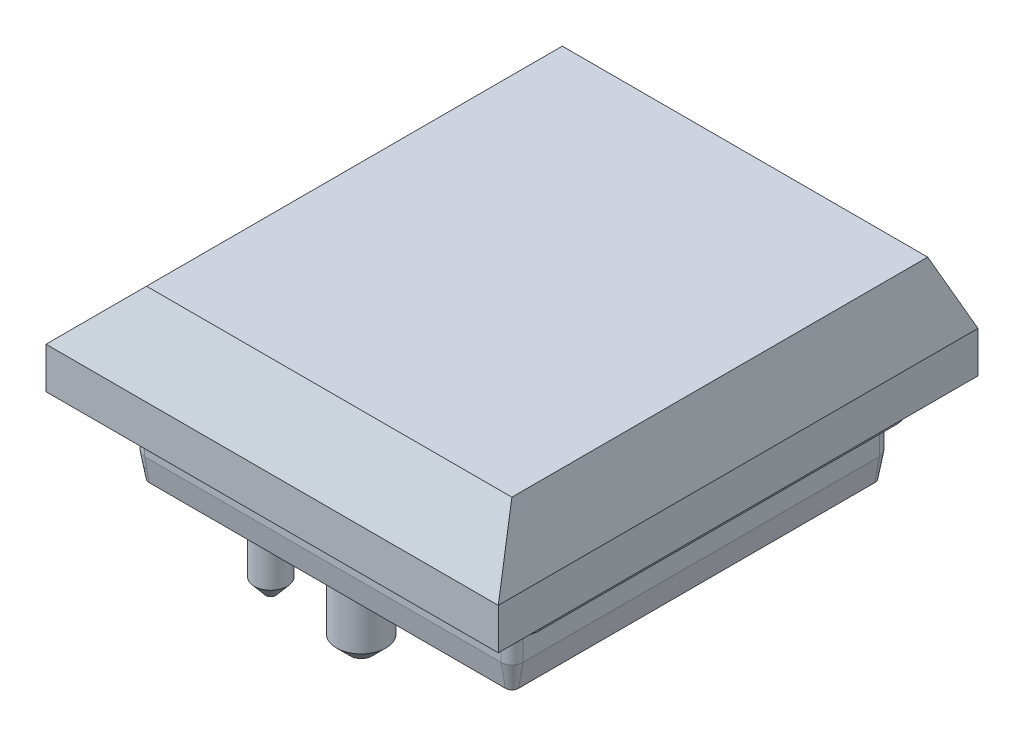
SolidWorks part; units mm, degrees
ref_plane "Front plane" through (0, 0, 0) normal (0, 0, 1) x (1, 0, 0)
ref_plane "Top plane" through (0, 0, 0) normal (0, 1, 0) x (1, 0, 0)
ref_plane "Right plane" through (0, 0, 0) normal (1, 0, 0) x (0, 0, -1)
sketch "Sketch1" plane through (0, 0, 0) normal (0, 1, 0) x (1, 0, 0)
  line L1 (-6.5, -7.5) -> (6.5, -7.5)
  line L2 (-7.5, -6.5) -> (-7.5, 6.5)
  line L3 (-6.5, 7.5) -> (6.5, 7.5)
  line L4 (7.5, -6.5) -> (7.5, 6.5)
  line L5 (-7.5, -7.5) -> (7.5, 7.5) construction
  line L6 (-7.5, 7.5) -> (7.5, -7.5) construction
  arc A0 (-7.5, 6.5) -> (-6.5, 7.5) centre (-6.5, 6.5) cw
  arc A1 (6.5, 7.5) -> (7.5, 6.5) centre (6.5, 6.5) cw
  arc A2 (6.5, -7.5) -> (7.5, -6.5) centre (6.5, -6.5) ccw
  arc A3 (-6.5, -7.5) -> (-7.5, -6.5) centre (-6.5, -6.5) cw
  point P0 (0, 0)
  dimension "D2" = 1
  dimension "D1" = 15
extrude "Boss-Extrude1" add sketch "Sketch1" along normal blind 0.8 contours L1 A2 L4 A1 L3 A0 L2 A3
sketch "Sketch2" plane through (0, 0, 0) normal (0, -1, 0) x (1, 0, 0)
  line L8 (-6.9, 6.5) -> (-6.9, -6.5)
  line L9 (-6.5, -6.9) -> (6.5, -6.9)
  line L10 (6.9, -6.5) -> (6.9, 6.5)
  line L11 (6.5, 6.9) -> (-6.5, 6.9)
  line L12 (-6.9, 6.5) -> (-6.9, -6.5)
  line L13 (-6.5, -6.9) -> (6.5, -6.9)
  line L14 (6.9, -6.5) -> (6.9, 6.5)
  line L15 (6.5, 6.9) -> (-6.5, 6.9)
  arc A8 (-6.5, 6.9) -> (-6.9, 6.5) centre (-6.5, 6.5) ccw
  arc A9 (-6.9, -6.5) -> (-6.5, -6.9) centre (-6.5, -6.5) ccw
  arc A10 (6.5, -6.9) -> (6.9, -6.5) centre (6.5, -6.5) ccw
  arc A11 (6.9, 6.5) -> (6.5, 6.9) centre (6.5, 6.5) ccw
  arc A12 (-6.5, 6.9) -> (-6.9, 6.5) centre (-6.5, 6.5) ccw
  arc A13 (-6.9, -6.5) -> (-6.5, -6.9) centre (-6.5, -6.5) ccw
  arc A14 (6.5, -6.9) -> (6.9, -6.5) centre (6.5, -6.5) ccw
  arc A15 (6.9, 6.5) -> (6.5, 6.9) centre (6.5, 6.5) ccw
  dimension "D1" = 0.6
extrude "Boss-Extrude2" add sketch "Sketch2" along normal blind 1.3
sketch "Sketch3" plane through (0, -1.3, 0) normal (0, -1, 0) x (1, 0, 0)
  line L4 (-6.9, 6.5) -> (-6.9, -6.5)
  line L5 (-6.5, -6.9) -> (6.5, -6.9)
  line L6 (6.9, -6.5) -> (6.9, 6.5)
  line L7 (6.5, 6.9) -> (-6.5, 6.9)
  line L8 (-6.9, 6.5) -> (-6.9, -6.5)
  line L9 (-6.5, -6.9) -> (6.5, -6.9)
  line L10 (6.9, -6.5) -> (6.9, 6.5)
  line L11 (6.5, 6.9) -> (-6.5, 6.9)
  arc A4 (-6.5, 6.9) -> (-6.9, 6.5) centre (-6.5, 6.5) ccw
  arc A5 (-6.9, -6.5) -> (-6.5, -6.9) centre (-6.5, -6.5) ccw
  arc A6 (6.5, -6.9) -> (6.9, -6.5) centre (6.5, -6.5) ccw
  arc A7 (6.9, 6.5) -> (6.5, 6.9) centre (6.5, 6.5) ccw
  arc A8 (-6.5, 6.9) -> (-6.9, 6.5) centre (-6.5, 6.5) ccw
  arc A9 (-6.9, -6.5) -> (-6.5, -6.9) centre (-6.5, -6.5) ccw
  arc A10 (6.5, -6.9) -> (6.9, -6.5) centre (6.5, -6.5) ccw
  arc A11 (6.9, 6.5) -> (6.5, 6.9) centre (6.5, 6.5) ccw
  dimension "D1" = 0
extrude "Boss-Extrude3" add sketch "Sketch3" along normal blind 0.9 draft 10
sketch "Sketch4" plane through (0, -2.2, 0) normal (0, -1, 0) x (1, 0, 0)
  line L0 (-5.9, 0) -> (6.1513, 0) construction
  circle A0 centre (0, 0) radius 1.6
  circle A1 centre (0, -5.5) radius 0.9
  circle A5 centre (0, 5.5) radius 0.9
  dimension "D1" = 3.2
  dimension "D2" = 1.8
  dimension "D3" = 5.5
extrude "Boss-Extrude4" add sketch "Sketch4" along normal blind 2.65
sketch "Sketch5" plane through (0, -2.2, 0) normal (0, -1, 0) x (1, 0, 0)
  line L0 (3.1075, 0) -> (-3.1075, 0) construction
  circle A0 centre (-5.9, 0) radius 0.6
  circle A1 centre (-3.8, -5) radius 0.6
  circle A2 centre (-3.8, 5) radius 0.6
  dimension "D1" = 1.2
  dimension "D2" = 3.8
  dimension "D3" = 5.9
  dimension "D4" = 5
extrude "Boss-Extrude5" add sketch "Sketch5" along normal blind 3
chamfer "Chamfer1" distance 0.5 angle 40 3 edges at (-3.8, -5.2, -5.6) (-5.9, -5.2, -0.6) (-3.8, -5.2, 5.6)
chamfer "Chamfer2" distance 0.5 angle 45 3 edges at (0, -4.85, -6.4) (0, -4.85, -1.6) (0, -4.85, 6.4)
sketch "Sketch6" plane through (0, 0.8, 0) normal (0, 1, 0) x (1, 0, 0)
  line L1 (8.25, 8.75) -> (-8.25, 8.75)
  line L2 (8.25, 8.75) -> (8.25, -8.75)
  line L3 (8.25, -8.75) -> (-8.25, -8.75)
  line L4 (-8.25, 8.75) -> (-8.25, -8.75)
  line L5 (8.25, 8.75) -> (-8.25, -8.75) construction
  line L6 (8.25, -8.75) -> (-8.25, 8.75) construction
  point P0 (0, 0)
  dimension "D1" = 16.5
  dimension "D2" = 17.5
extrude "Boss-Extrude6" add sketch "Sketch6" along normal blind 4
chamfer "Chamfer3" distance 2.5 angle 15 1 edges at (8.25, 4.8, 0)
chamfer "Chamfer4" distance 2.5 angle 25 2 edges at (-0.3349, 4.8, -8.75) (-0.3349, 4.8, 8.75)
chamfer "Chamfer5" distance 2.5 angle 45 1 edges at (-8.25, 4.8, 0)
ref_plane "Vertical" through (0, 0, 0) normal (0, 0, 1) x (1, 0, 0)
ref_plane "Horisontal" through (0, 0, 0) normal (1, 0, 0) x (0, 0, -1)
